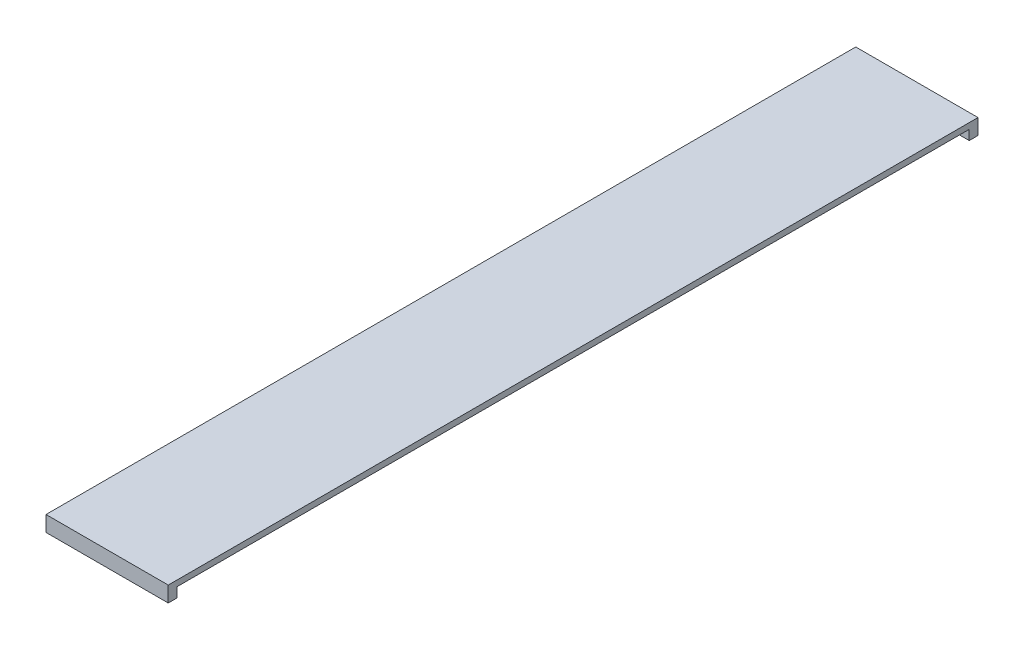
SolidWorks part; units mm, degrees
material "Polyurethane Foam Rigid"
ref_plane "Front Plane" through (0, 0, 0) normal (0, 0, 1) x (1, 0, 0)
ref_plane "Top Plane" through (0, 0, 0) normal (0, 1, 0) x (1, 0, 0)
ref_plane "Right Plane" through (0, 0, 0) normal (1, 0, 0) x (0, 0, -1)
sketch "Sketch1" plane through (0, 0, 0) normal (1, 0, 0) x (0, 0, -1)
  line L0 (-1292.225, -31.75) -> (-1320.8, -31.75)
  line L1 (-1320.8, -31.75) -> (-1320.8, 19.05)
  line L2 (-1320.8, 19.05) -> (1320.8, 19.05)
  line L3 (1320.8, 19.05) -> (1320.8, -31.75)
  line L4 (1320.8, -31.75) -> (1292.225, -31.75)
  line L5 (1292.225, -31.75) -> (1292.225, 0)
  line L6 (1292.225, 0) -> (-1292.225, 0)
  line L7 (-1292.225, 0) -> (-1292.225, -31.75)
  point P5 (0, 0)
  point P11 (0, 19.05)
  point P12 (1306.5125, -31.75)
  point P13 (-1292.225, -18.87)
  dimension "D1" = 2584.45
  dimension "D2" = 2641.6
  dimension "D3" = 50.8
  dimension "D4" = 19.05
extrude "Boss-Extrude1" add sketch "Sketch1" along normal blind 398.78
